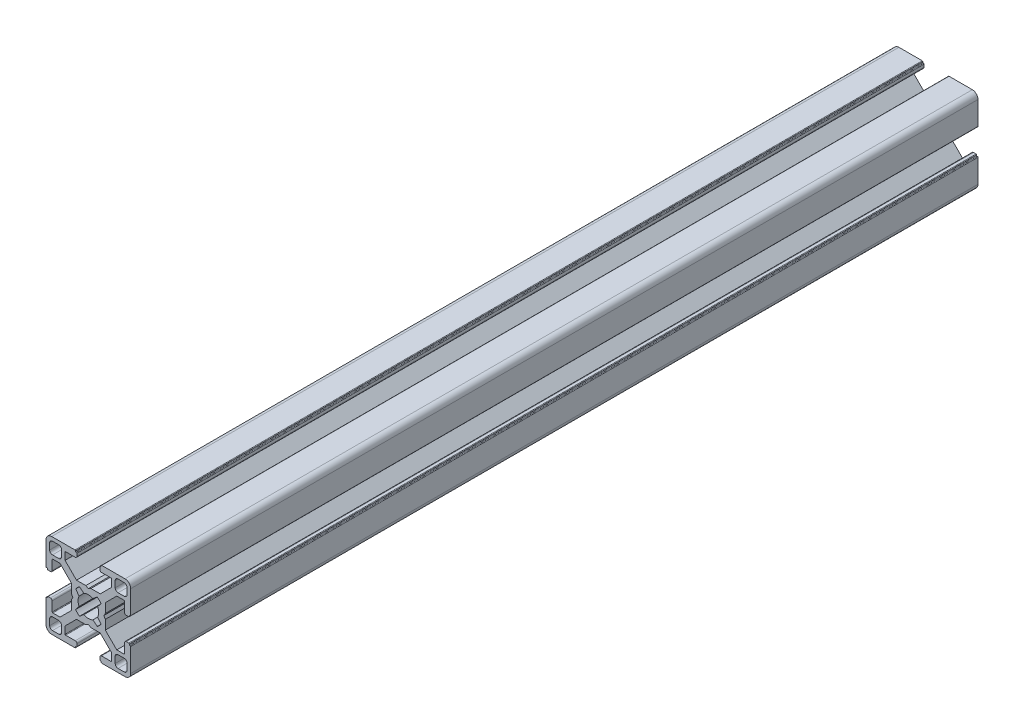
SolidWorks part; units mm, degrees
material "АД31 ГОСТ 4784-97"
ref_plane "Front" through (0, 0, 0) normal (0, 0, 1) x (1, 0, 0)
ref_plane "Top" through (0, 0, 0) normal (0, 1, 0) x (1, 0, 0)
ref_plane "Right" through (0, 0, 0) normal (1, 0, 0) x (0, 0, -1)
sketch "Sketch1" plane through (0, 0, 0) normal (0, 0, 1) x (1, 0, 0)
  line L0 (13.7, 12.7) -> (13.7, 10.5)
  line L1 (10.5, 9.5) -> (12.7, 9.5)
  line L2 (9.5, 12.7) -> (9.5, 10.5)
  line L3 (10.5, 13.7) -> (12.7, 13.7)
  line L4 (3.1359, 4.5184) -> (1.6001, 3.2806)
  line L5 (3.2806, 1.6001) -> (4.5053, 3.1547)
  line L6 (6.0045, 0.9) -> (5.4849, 0)
  line L7 (6.0045, 4.2045) -> (6.0045, 0.9)
  line L8 (0, -5.4849) -> (0.9, -6)
  line L9 (0.9, -6) -> (4.2045, -6)
  line L10 (4.2045, -6) -> (8.25, -10.05)
  line L11 (8.25, -10.05) -> (8.25, -12.6)
  line L12 (4.65, -12.8) -> (8.05, -12.8)
  line L13 (4.05, -14.3) -> (4.05, -13.4)
  line L14 (4.25, -14.5) -> (4.35, -14.5)
  line L15 (4.55, -14.8) -> (4.55, -14.7)
  line L16 (4.75, -15) -> (13, -15)
  line L17 (15, -13) -> (15, -4.75)
  line L18 (14.7, -4.55) -> (14.8, -4.55)
  line L19 (14.5, -4.35) -> (14.5, -4.25)
  line L20 (13.4, -4.05) -> (14.3, -4.05)
  line L21 (12.8, -8.05) -> (12.8, -4.65)
  line L22 (12.6, -8.25) -> (10.05, -8.25)
  line L23 (10.05, -8.25) -> (6.0045, -4.2045)
  line L24 (6.0045, -4.2045) -> (6.0045, -0.9)
  line L25 (6.0045, -0.9) -> (5.4849, 0)
  line L26 (10.05, 8.25) -> (6.0045, 4.2045)
  line L27 (12.6, 8.25) -> (10.05, 8.25)
  line L28 (12.8, 8.05) -> (12.8, 4.65)
  line L29 (13.4, 4.05) -> (14.3, 4.05)
  line L30 (14.5, 4.35) -> (14.5, 4.25)
  line L31 (14.7, 4.55) -> (14.8, 4.55)
  line L32 (15, 13) -> (15, 4.75)
  line L33 (4.75, 15) -> (13, 15)
  line L34 (4.55, 14.8) -> (4.55, 14.7)
  line L35 (4.25, 14.5) -> (4.35, 14.5)
  line L36 (4.05, 14.3) -> (4.05, 13.4)
  line L37 (4.65, 12.8) -> (8.05, 12.8)
  line L38 (8.25, 10.05) -> (8.25, 12.6)
  line L39 (4.2045, 6) -> (8.25, 10.05)
  line L40 (0.9, 6) -> (4.2045, 6)
  line L41 (0, 5.4849) -> (0.9, 6)
  line L42 (-13.7, -12.7) -> (-13.7, -10.5)
  line L43 (-10.5, -9.5) -> (-12.7, -9.5)
  line L44 (-9.5, -12.7) -> (-9.5, -10.5)
  line L45 (-10.5, -13.7) -> (-12.7, -13.7)
  line L46 (-3.1359, -4.5184) -> (-1.6001, -3.2806)
  line L47 (-3.2806, -1.6001) -> (-4.5053, -3.1547)
  line L48 (0, 5.4849) -> (-0.9, 6)
  line L49 (-0.9, 6) -> (-4.2045, 6)
  line L50 (-4.2045, 6) -> (-8.25, 10.05)
  line L51 (-8.25, 10.05) -> (-8.25, 12.6)
  line L52 (-4.65, 12.8) -> (-8.05, 12.8)
  line L53 (-4.05, 14.3) -> (-4.05, 13.4)
  line L54 (-4.25, 14.5) -> (-4.35, 14.5)
  line L55 (-4.55, 14.8) -> (-4.55, 14.7)
  line L56 (-4.75, 15) -> (-13, 15)
  line L57 (-15, 13) -> (-15, 4.75)
  line L58 (-14.7, 4.55) -> (-14.8, 4.55)
  line L59 (-14.5, 4.35) -> (-14.5, 4.25)
  line L60 (-13.4, 4.05) -> (-14.3, 4.05)
  line L61 (-12.8, 8.05) -> (-12.8, 4.65)
  line L62 (-12.6, 8.25) -> (-10.05, 8.25)
  line L63 (-10.05, 8.25) -> (-6.0045, 4.2045)
  line L64 (-6.0045, -0.9) -> (-5.4849, 0)
  line L65 (-6.0045, -4.2045) -> (-6.0045, -0.9)
  line L66 (-10.05, -8.25) -> (-6.0045, -4.2045)
  line L67 (-12.6, -8.25) -> (-10.05, -8.25)
  line L68 (-12.8, -8.05) -> (-12.8, -4.65)
  line L69 (-13.4, -4.05) -> (-14.3, -4.05)
  line L70 (-14.5, -4.35) -> (-14.5, -4.25)
  line L71 (-14.7, -4.55) -> (-14.8, -4.55)
  line L72 (-15, -13) -> (-15, -4.75)
  line L73 (-4.75, -15) -> (-13, -15)
  line L74 (-4.55, -14.8) -> (-4.55, -14.7)
  line L75 (-4.25, -14.5) -> (-4.35, -14.5)
  line L76 (-4.05, -14.3) -> (-4.05, -13.4)
  line L77 (3.2806, -1.6001) -> (4.5053, -3.1547)
  line L78 (3.1359, -4.5184) -> (1.6001, -3.2806)
  line L79 (-4.65, -12.8) -> (-8.05, -12.8)
  line L80 (-8.25, -10.05) -> (-8.25, -12.6)
  line L81 (-4.2045, -6) -> (-8.25, -10.05)
  line L82 (-0.9, -6) -> (-4.2045, -6)
  line L83 (0, -5.4849) -> (-0.9, -6)
  line L84 (10.5, -13.7) -> (12.7, -13.7)
  line L85 (9.5, -12.7) -> (9.5, -10.5)
  line L86 (10.5, -9.5) -> (12.7, -9.5)
  line L87 (13.7, -12.7) -> (13.7, -10.5)
  line L88 (-6.0045, 4.2045) -> (-6.0045, 0.9)
  line L89 (-6.0045, 0.9) -> (-5.4849, 0)
  line L90 (-3.2806, 1.6001) -> (-4.5053, 3.1547)
  line L91 (-3.1359, 4.5184) -> (-1.6001, 3.2806)
  line L92 (-10.5, 13.7) -> (-12.7, 13.7)
  line L93 (-9.5, 12.7) -> (-9.5, 10.5)
  line L94 (-10.5, 9.5) -> (-12.7, 9.5)
  line L95 (-13.7, 12.7) -> (-13.7, 10.5)
  line L96 (-23.4857, 0) -> (20.9308, 0) construction
  line L97 (0, 17.9563) -> (0, -17.361) construction
  arc A0 (13.7, 12.7) -> (12.7, 13.7) centre (12.7, 12.7) ccw
  arc A1 (12.7, 9.5) -> (13.7, 10.5) centre (12.7, 10.5) ccw
  arc A2 (9.5, 10.5) -> (10.5, 9.5) centre (10.5, 10.5) ccw
  arc A3 (10.5, 13.7) -> (9.5, 12.7) centre (10.5, 12.7) ccw
  arc A4 (1.6001, 3.2806) -> (-1.6001, 3.2806) centre (0, 0) ccw
  arc A5 (8.25, -12.6) -> (8.05, -12.8) centre (8.05, -12.6) cw
  arc A6 (4.65, -12.8) -> (4.05, -13.4) centre (4.65, -13.4) ccw
  arc A7 (4.05, -14.3) -> (4.25, -14.5) centre (4.25, -14.3) ccw
  arc A8 (4.35, -14.5) -> (4.55, -14.7) centre (4.35, -14.7) cw
  arc A9 (4.55, -14.8) -> (4.75, -15) centre (4.75, -14.8) ccw
  arc A10 (13, -15) -> (15, -13) centre (13, -13) ccw
  arc A11 (15, -4.75) -> (14.8, -4.55) centre (14.8, -4.75) ccw
  arc A12 (14.7, -4.55) -> (14.5, -4.35) centre (14.7, -4.35) cw
  arc A13 (14.5, -4.25) -> (14.3, -4.05) centre (14.3, -4.25) ccw
  arc A14 (13.4, -4.05) -> (12.8, -4.65) centre (13.4, -4.65) ccw
  arc A15 (12.8, -8.05) -> (12.6, -8.25) centre (12.6, -8.05) cw
  arc A16 (4.5053, 3.1547) -> (3.1359, 4.5184) centre (0, 0) ccw
  arc A17 (12.8, 8.05) -> (12.6, 8.25) centre (12.6, 8.05) ccw
  arc A18 (13.4, 4.05) -> (12.8, 4.65) centre (13.4, 4.65) cw
  arc A19 (14.5, 4.25) -> (14.3, 4.05) centre (14.3, 4.25) cw
  arc A20 (14.7, 4.55) -> (14.5, 4.35) centre (14.7, 4.35) ccw
  arc A21 (15, 4.75) -> (14.8, 4.55) centre (14.8, 4.75) cw
  arc A22 (13, 15) -> (15, 13) centre (13, 13) cw
  arc A23 (4.55, 14.8) -> (4.75, 15) centre (4.75, 14.8) cw
  arc A24 (4.35, 14.5) -> (4.55, 14.7) centre (4.35, 14.7) ccw
  arc A25 (4.05, 14.3) -> (4.25, 14.5) centre (4.25, 14.3) cw
  arc A26 (4.65, 12.8) -> (4.05, 13.4) centre (4.65, 13.4) cw
  arc A27 (8.25, 12.6) -> (8.05, 12.8) centre (8.05, 12.6) ccw
  arc A28 (-13.7, -12.7) -> (-12.7, -13.7) centre (-12.7, -12.7) ccw
  arc A29 (-12.7, -9.5) -> (-13.7, -10.5) centre (-12.7, -10.5) ccw
  arc A30 (-9.5, -10.5) -> (-10.5, -9.5) centre (-10.5, -10.5) ccw
  arc A31 (-10.5, -13.7) -> (-9.5, -12.7) centre (-10.5, -12.7) ccw
  arc A32 (-4.5053, -3.1547) -> (-3.1359, -4.5184) centre (0, 0) ccw
  arc A33 (-3.2806, 1.6001) -> (-3.2806, -1.6001) centre (0, 0) ccw
  arc A34 (-8.25, 12.6) -> (-8.05, 12.8) centre (-8.05, 12.6) cw
  arc A35 (-4.65, 12.8) -> (-4.05, 13.4) centre (-4.65, 13.4) ccw
  arc A36 (-4.05, 14.3) -> (-4.25, 14.5) centre (-4.25, 14.3) ccw
  arc A37 (-4.35, 14.5) -> (-4.55, 14.7) centre (-4.35, 14.7) cw
  arc A38 (-4.55, 14.8) -> (-4.75, 15) centre (-4.75, 14.8) ccw
  arc A39 (-13, 15) -> (-15, 13) centre (-13, 13) ccw
  arc A40 (-15, 4.75) -> (-14.8, 4.55) centre (-14.8, 4.75) ccw
  arc A41 (-14.7, 4.55) -> (-14.5, 4.35) centre (-14.7, 4.35) cw
  arc A42 (-14.5, 4.25) -> (-14.3, 4.05) centre (-14.3, 4.25) ccw
  arc A43 (-13.4, 4.05) -> (-12.8, 4.65) centre (-13.4, 4.65) ccw
  arc A44 (-12.8, 8.05) -> (-12.6, 8.25) centre (-12.6, 8.05) cw
  arc A45 (-4.5053, 3.1547) -> (-3.1359, 4.5184) centre (0, 0) cw
  arc A46 (-12.8, -8.05) -> (-12.6, -8.25) centre (-12.6, -8.05) ccw
  arc A47 (-13.4, -4.05) -> (-12.8, -4.65) centre (-13.4, -4.65) cw
  arc A48 (-14.5, -4.25) -> (-14.3, -4.05) centre (-14.3, -4.25) cw
  arc A49 (3.2806, 1.6001) -> (3.2806, -1.6001) centre (0, 0) cw
  arc A50 (4.5053, -3.1547) -> (3.1359, -4.5184) centre (0, 0) cw
  arc A51 (1.6001, -3.2806) -> (-1.6001, -3.2806) centre (0, 0) cw
  arc A52 (-14.7, -4.55) -> (-14.5, -4.35) centre (-14.7, -4.35) ccw
  arc A53 (-15, -4.75) -> (-14.8, -4.55) centre (-14.8, -4.75) cw
  arc A54 (-13, -15) -> (-15, -13) centre (-13, -13) cw
  arc A55 (-4.55, -14.8) -> (-4.75, -15) centre (-4.75, -14.8) cw
  arc A56 (10.5, -13.7) -> (9.5, -12.7) centre (10.5, -12.7) cw
  arc A57 (9.5, -10.5) -> (10.5, -9.5) centre (10.5, -10.5) cw
  arc A58 (12.7, -9.5) -> (13.7, -10.5) centre (12.7, -10.5) cw
  arc A59 (13.7, -12.7) -> (12.7, -13.7) centre (12.7, -12.7) cw
  arc A60 (-4.35, -14.5) -> (-4.55, -14.7) centre (-4.35, -14.7) ccw
  arc A61 (-4.05, -14.3) -> (-4.25, -14.5) centre (-4.25, -14.3) cw
  arc A62 (-4.65, -12.8) -> (-4.05, -13.4) centre (-4.65, -13.4) cw
  arc A63 (-8.25, -12.6) -> (-8.05, -12.8) centre (-8.05, -12.6) ccw
  arc A64 (-10.5, 13.7) -> (-9.5, 12.7) centre (-10.5, 12.7) cw
  arc A65 (-9.5, 10.5) -> (-10.5, 9.5) centre (-10.5, 10.5) cw
  arc A66 (-12.7, 9.5) -> (-13.7, 10.5) centre (-12.7, 10.5) cw
  arc A67 (-13.7, 12.7) -> (-12.7, 13.7) centre (-12.7, 12.7) cw
  point P81 (15, 15)
  point P82 (0, 15)
  point P203 (0, -15)
  point P204 (15, -15)
  point P206 (0, 0)
  point P207 (15, 0)
  point P219 (-15, 0)
  point P220 (-15, -15)
  point P221 (-15, 15)
  dimension "D6" = 7.3
  dimension "D7" = 11
  dimension "D1" = 30
  dimension "D2" = 15
  dimension "D3" = 30
  dimension "D4" = 8.1
  dimension "D5" = 9
  dimension "D8" = 8.1
extrude "Base-Extrude" add sketch "Sketch1" against normal blind 300
